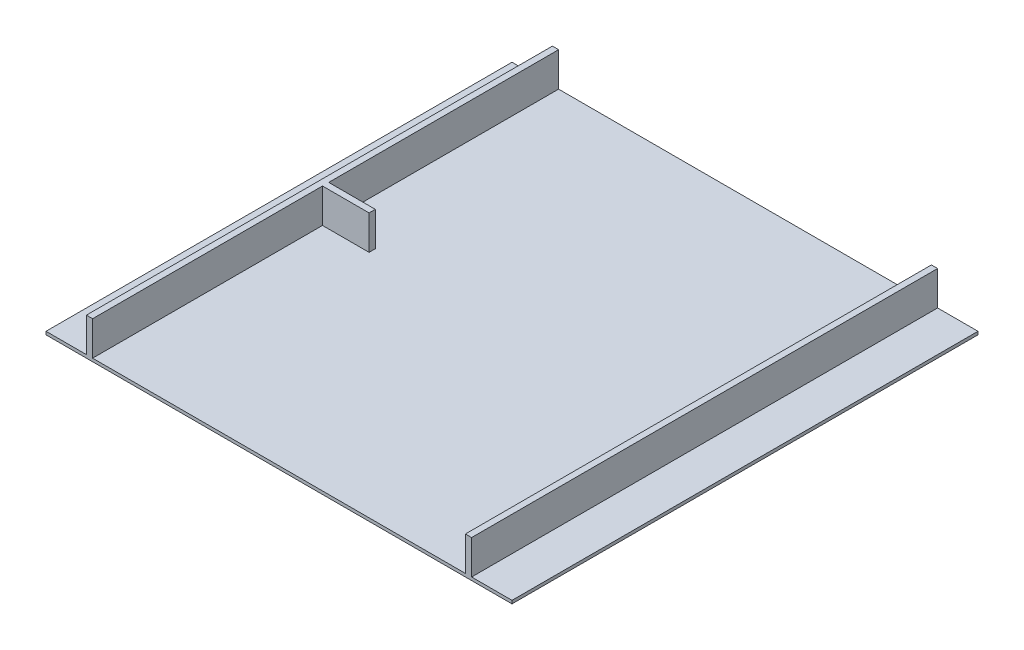
SolidWorks part; units mm, degrees
ref_plane "Front Plane" through (0, 0, 0) normal (0, 0, 1) x (1, 0, 0)
ref_plane "Top Plane" through (0, 0, 0) normal (0, 1, 0) x (1, 0, 0)
ref_plane "Right Plane" through (0, 0, 0) normal (1, 0, 0) x (0, 0, -1)
sketch "Sketch2" plane through (0, 0, 0) normal (0, 1, 0) x (1, 0, 0)
  line L1 (-750, 750) -> (750, 750)
  line L2 (-750, 750) -> (-750, -750)
  line L3 (-750, -750) -> (750, -750)
  line L4 (750, 750) -> (750, -750)
  line L5 (-750, 750) -> (750, -750) construction
  line L6 (-750, -750) -> (750, 750) construction
  point P0 (0, 0)
  dimension "D1" = 1500
  dimension "D2" = 1500
extrude "Boss-Extrude1" add sketch "Sketch2" along normal blind 10
sketch "Sketch3" plane through (0, 10, 0) normal (0, 1, 0) x (1, 0, 0)
  line L0 (620, 750) -> (620, -750) construction
  line L1 (750, 750) -> (-750, 750) construction
  line L2 (-750, -750) -> (750, -750) construction
  line L3 (600, 750) -> (600, -750) construction
  line L4 (750, -750) -> (750, 750) construction
  line L5 (-750, -600) -> (750, -600) construction
  line L6 (-750, 750) -> (-750, -750) construction
  line L7 (-750, -620) -> (750, -620) construction
  line L8 (-750, 0) -> (750, 0) construction
  line L9 (0, 750) -> (0, -750) construction
  line L10 (-750, 620) -> (750, 620) construction
  line L11 (-750, 600) -> (750, 600) construction
  line L12 (-620, 750) -> (-620, -750) construction
  line L13 (-600, 750) -> (-600, -750) construction
  line L15 (-620, 750) -> (-600, 750)
  line L16 (-620, 750) -> (-620, -750)
  line L17 (-620, -750) -> (-600, -750)
  line L18 (-600, 750) -> (-600, -750)
  line L19 (600, 750) -> (620, 750)
  line L20 (600, 750) -> (600, -750)
  line L21 (600, -750) -> (620, -750)
  line L22 (620, 750) -> (620, -750)
  line L23 (-600, 10) -> (-450, 10)
  line L24 (-600, 10) -> (-600, -10)
  line L25 (-600, -10) -> (-450, -10)
  line L26 (-450, 10) -> (-450, -10)
  line L27 (-600, 10) -> (-450, -10) construction
  line L28 (-600, -10) -> (-450, 10) construction
  point P0 (-525, 0)
  line M4 (750, 750) -> (-750, 750)
  line M6 (-750, -750) -> (750, -750)
  dimension "D6" = 150
  dimension "D5" = 20
  dimension "D7" = 20
  dimension "D8" = 150
  dimension "D1" = 20
extrude "Boss-Extrude2" add sketch "Sketch3" along normal blind 110 contours L18 L16 M4 M6 | L26 L23 L18 L25 | L22 L20 M4 M6
equation "\"CellSize\"=1500"
equation "\"D1@Sketch2\"=\"CellSize\""
equation "\"D2@Sketch2\"=\"CellSize\""
equation "\"TrackWidth\"= 1200"
equation "\"C\"=342.079"
equation "\"WallWidth\"=20"
equation "\"D6@Sketch3\"=\"EdgeWidth\""
equation "\"D5@Sketch3\"=\"WallWidth\""
equation "\"D7@Sketch3\"=\"WallWidth\""
equation "\"EdgeWidth\"= ( \"CellSize\" - \"TrackWidth\" ) / 2"
equation "\"D8@Sketch3\"=\"EdgeWidth\""
equation "\"D1@Sketch3\"=\"WallWidth\""
equation "\"ObstacleWidth\"=150"
equation "\"D2@Sketch3\"=\"ObstacleWidth\""
